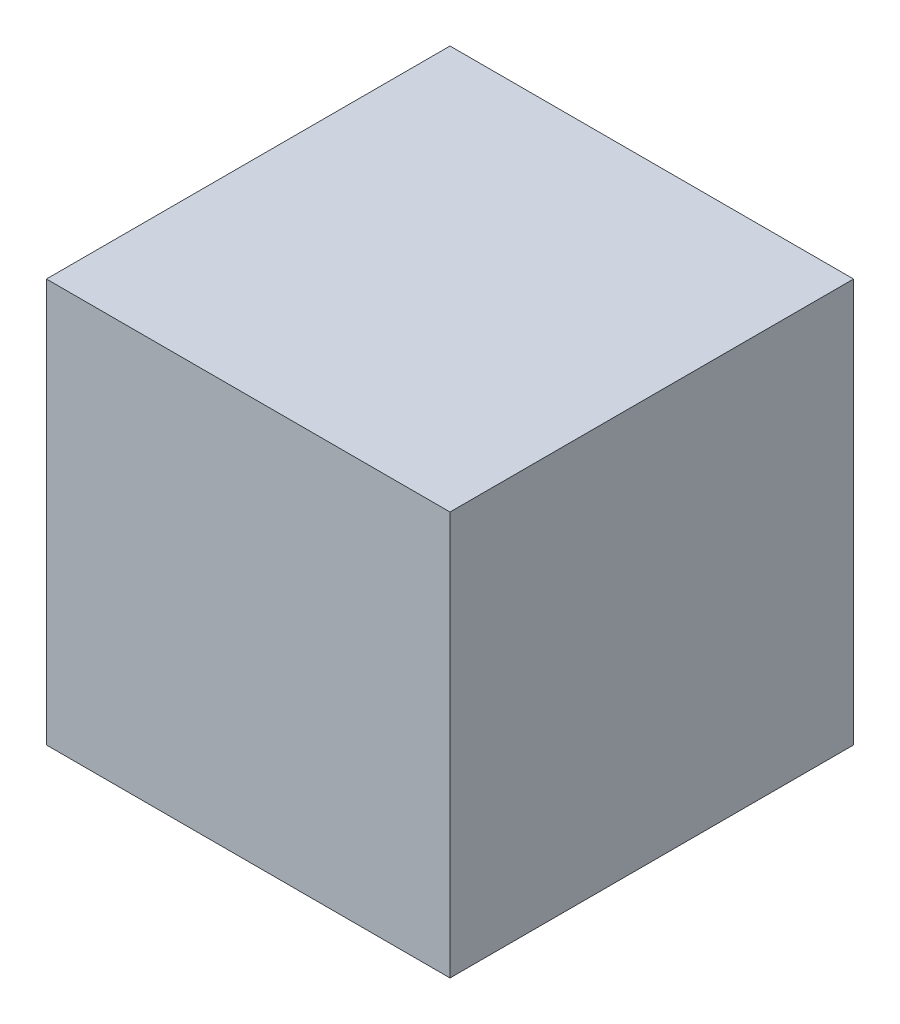
SolidWorks part; units mm, degrees
ref_plane "Front Plane" through (0, 0, 0) normal (0, 0, 1) x (1, 0, 0)
ref_plane "Top Plane" through (0, 0, 0) normal (0, 1, 0) x (1, 0, 0)
ref_plane "Right Plane" through (0, 0, 0) normal (1, 0, 0) x (0, 0, -1)
sketch "Sketch1" plane through (0, 0, 0) normal (0, 1, 0) x (1, 0, 0)
  line L1 (0, 0) -> (228.6, 0)
  line L2 (0, 0) -> (0, 228.6)
  line L3 (0, 228.6) -> (228.6, 228.6)
  line L4 (228.6, 0) -> (228.6, 228.6)
  dimension "D1" = 228.6
  dimension "D2" = 228.6
extrude "Extrude1" add sketch "Sketch1" along normal blind 228.6
